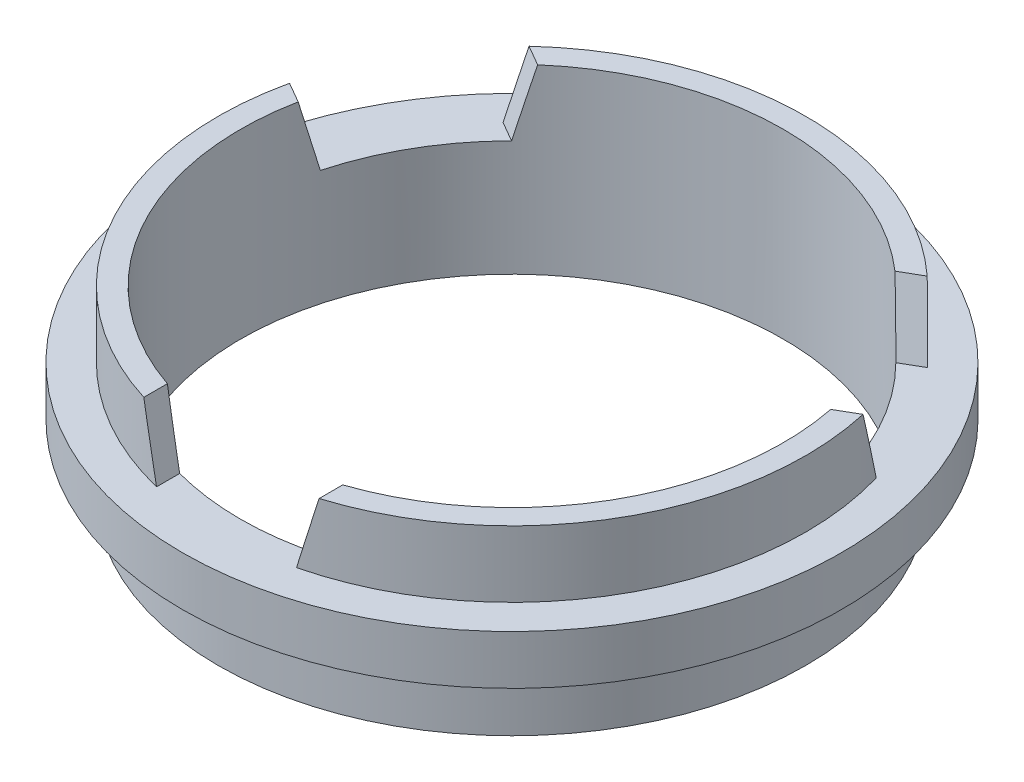
SolidWorks part; units mm, degrees
ref_plane "Front Plane" through (0, 0, 0) normal (0, 0, 1) x (1, 0, 0)
ref_plane "Top Plane" through (0, 0, 0) normal (0, 1, 0) x (1, 0, 0)
ref_plane "Right Plane" through (0, 0, 0) normal (1, 0, 0) x (0, 0, -1)
sketch "Sketch1" plane through (0, 0, 0) normal (0, 1, 0) x (1, 0, 0)
  circle A0 centre (0, 0) radius 9.7
  dimension "D1" = 19.4
extrude "Boss-Extrude1" add sketch "Sketch1" along normal blind 5.35
sketch "Sketch2" plane through (0, 5.35, 0) normal (0, 1, 0) x (1, 0, 0)
  circle A0 centre (0, 0) radius 8.65
  circle A1 centre (0, 0) radius 9.7
  dimension "D1" = 17.3
extrude "Cut-Extrude1" cut sketch "Sketch2" against normal blind 1.95
sketch "Sketch3" plane through (0, 0, 0) normal (0, -1, 0) x (1, 0, 0)
  circle A0 centre (0, 0) radius 8.65
  circle A1 centre (0, 0) radius 9.7
  dimension "D1" = 17.3
extrude "Cut-Extrude2" cut sketch "Sketch3" against normal blind 1.95
sketch "Sketch4" plane through (0, 3.4, 0) normal (0, 1, 0) x (1, 0, 0)
  line L1 (0, -2.9425) -> (0, 2.9425) construction
  arc A0 (-1.8, 9.5315) -> (1.8, 9.5315) centre (0, 10.9285) ccw
  circle A3 centre (0, 0) radius 9.7 construction
  circle A4 centre (0, 0) radius 8.65 construction
  point P5 (0, 0)
  point P8 (0, 0)
  point P9 (0, 0)
  dimension "D1" = 1.8
  dimension "D2" = 1.8
extrude "Cut-Extrude3" cut sketch "Sketch4" against normal blind 1.95 and the other way through all
sketch "Sketch5" plane through (0, 5.35, 0) normal (0, 1, 0) x (1, 0, 0)
  circle A0 centre (0, 0) radius 7.99
  dimension "D1" = 15.98
extrude "Cut-Extrude4" cut sketch "Sketch5" against normal through all
sketch "Sketch6" plane through (0, 0, 0) normal (0, 0, 1) x (1, 0, 0)
  line L0 (0, 3.4) -> (-2.06, 3.4)
  line L1 (0, -2.9425) -> (0, 2.9425) construction
  line L2 (0, 3.4) -> (2.06, 3.4)
  line L3 (9.7, 3.4) -> (-9.7, 3.4) construction
  line L4 (0, 5.35) -> (-2.58, 5.35)
  line L5 (7.99, 5.35) -> (-7.99, 5.35) construction
  line L6 (0, 5.35) -> (2.58, 5.35)
  line L7 (-2.06, 3.4) -> (-2.58, 5.35)
  line L8 (2.06, 3.4) -> (2.58, 5.35)
  dimension "D1" = 2.06
  dimension "D2" = 2.06
  dimension "D3" = 2.58
  dimension "D4" = 2.58
extrude "Cut-Extrude5" cut sketch "Sketch6" along normal through all
pattern_circular "CirPattern1" count 3 over 360 about axis through (0, 0, 0) along (0, 1, 0) of "Cut-Extrude5"
